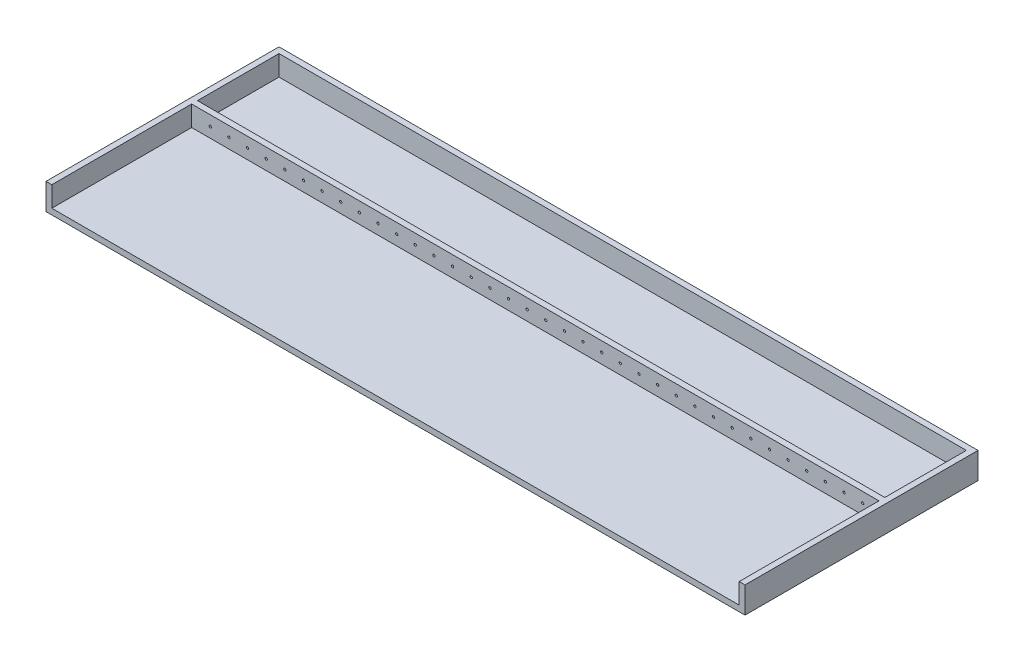
SolidWorks part; units mm, degrees
material "PVC 0.007 Plasticized"
ref_plane "Front Plane" through (0, 0, 0) normal (0, 0, 1) x (1, 0, 0)
ref_plane "Top Plane" through (0, 0, 0) normal (0, 1, 0) x (1, 0, 0)
ref_plane "Right Plane" through (0, 0, 0) normal (1, 0, 0) x (0, 0, -1)
sketch "Sketch1" plane through (0, 0, 0) normal (0, 1, 0) x (1, 0, 0)
  line L1 (0, 0) -> (600, 0)
  line L2 (0, 0) -> (0, 200)
  line L3 (0, 200) -> (600, 200)
  line L4 (600, 0) -> (600, 200)
  dimension "D1" = 600
  dimension "D2" = 200
extrude "Boss-Extrude1" add sketch "Sketch1" along normal blind 5
sketch "Sketch2" plane through (0, 5, 0) normal (0, 1, 0) x (1, 0, 0)
  line L0 (0, 0) -> (600, 0) construction
  line L1 (0, 200) -> (5, 200)
  line L2 (0, 200) -> (0, 0)
  line L3 (0, 0) -> (5, 0)
  line L4 (5, 195) -> (5, 125)
  line L5 (600, 200) -> (0, 200) construction
  line L6 (600, 0) -> (595, 0)
  line L7 (600, 0) -> (600, 200)
  line L8 (600, 200) -> (595, 200)
  line L9 (595, 0) -> (595, 120)
  line L10 (5, 120) -> (5, 0)
  line L11 (5, 200) -> (595, 200)
  line L13 (5, 195) -> (595, 195)
  line L15 (5, 125) -> (595, 125)
  line L17 (5, 120) -> (595, 120)
  line L19 (595, 125) -> (595, 195)
  dimension "D1" = 5
  dimension "D2" = 5
  dimension "D3" = 5
  dimension "D4" = 80
  dimension "D5" = 75
extrude "Boss-Extrude2" add sketch "Sketch2" along normal blind 17.5
sketch "Sketch3" plane through (0, 0, -120) normal (0, 0, 1) x (1, 0, 0)
  line L0 (5, 5) -> (595, 5) construction
  line L1 (5, 22.5) -> (5, 5) construction
  circle A0 centre (21, 13.75) radius 1
  circle A1 centre (37, 13.75) radius 1
  circle A2 centre (53, 13.75) radius 1
  circle A3 centre (69, 13.75) radius 1
  circle A4 centre (85, 13.75) radius 1
  circle A5 centre (101, 13.75) radius 1
  circle A6 centre (117, 13.75) radius 1
  circle A7 centre (133, 13.75) radius 1
  circle A8 centre (149, 13.75) radius 1
  circle A9 centre (165, 13.75) radius 1
  circle A10 centre (181, 13.75) radius 1
  circle A11 centre (197, 13.75) radius 1
  circle A12 centre (213, 13.75) radius 1
  circle A13 centre (229, 13.75) radius 1
  circle A14 centre (245, 13.75) radius 1
  circle A15 centre (261, 13.75) radius 1
  circle A16 centre (277, 13.75) radius 1
  circle A17 centre (293, 13.75) radius 1
  circle A18 centre (309, 13.75) radius 1
  circle A19 centre (325, 13.75) radius 1
  circle A20 centre (341, 13.75) radius 1
  circle A21 centre (357, 13.75) radius 1
  circle A22 centre (373, 13.75) radius 1
  circle A23 centre (389, 13.75) radius 1
  circle A24 centre (405, 13.75) radius 1
  circle A25 centre (421, 13.75) radius 1
  circle A26 centre (437, 13.75) radius 1
  circle A27 centre (453, 13.75) radius 1
  circle A28 centre (469, 13.75) radius 1
  circle A29 centre (485, 13.75) radius 1
  circle A30 centre (501, 13.75) radius 1
  circle A31 centre (517, 13.75) radius 1
  circle A32 centre (533, 13.75) radius 1
  circle A33 centre (549, 13.75) radius 1
  circle A34 centre (565, 13.75) radius 1
  circle A35 centre (581, 13.75) radius 1
  dimension "D1" = 2
  dimension "D2" = 8.75
  dimension "D3" = 16
  dimension "D4" = 36
extrude "Cut-Extrude1" cut sketch "Sketch3" against normal blind 5
